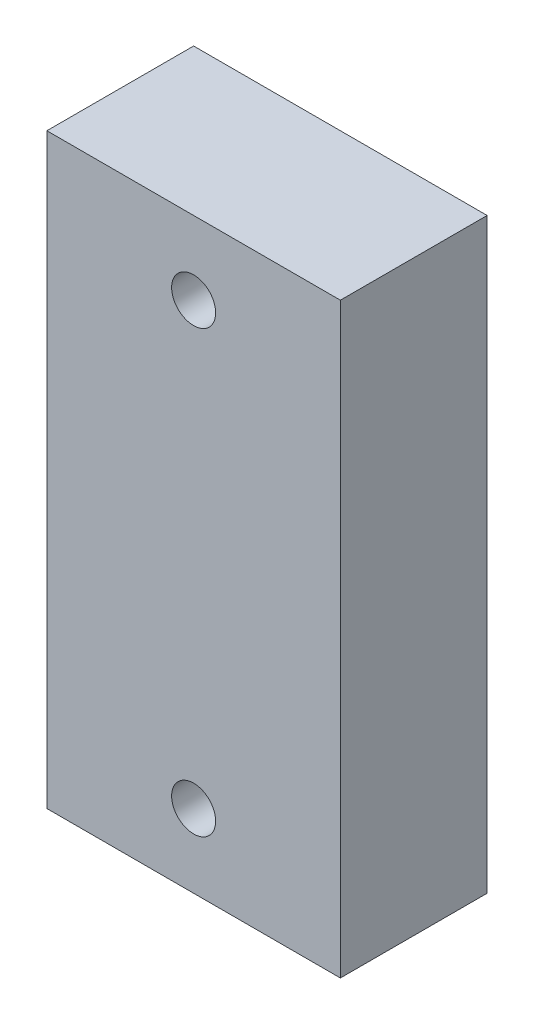
SolidWorks part; units mm, degrees
ref_plane "Plan de face" through (0, 0, 0) normal (0, 0, 1) x (1, 0, 0)
ref_plane "Plan de dessus" through (0, 0, 0) normal (0, 1, 0) x (1, 0, 0)
ref_plane "Plan de droite" through (0, 0, 0) normal (1, 0, 0) x (0, 0, -1)
sketch "Esquisse1" plane through (0, 0, 0) normal (0, 0, 1) x (1, 0, 0)
  line L0 (-20, 20) -> (0, 20) construction
  line L1 (0, 0) -> (-20, 0)
  line L2 (0, 0) -> (0, 40)
  line L3 (0, 40) -> (-20, 40)
  line L4 (-20, 0) -> (-20, 40)
  circle A0 centre (-10, 35) radius 1.5
  circle A1 centre (-10, 5) radius 1.5
  dimension "D5" = 3
  dimension "D6" = 3
  dimension "D1" = 20
  dimension "D2" = 40
  dimension "D3" = 15
  dimension "D4" = 15
  dimension "D7" = 10
  dimension "D8" = 10
extrude "Boss.-Extru.1" add sketch "Esquisse1" along normal blind 10
